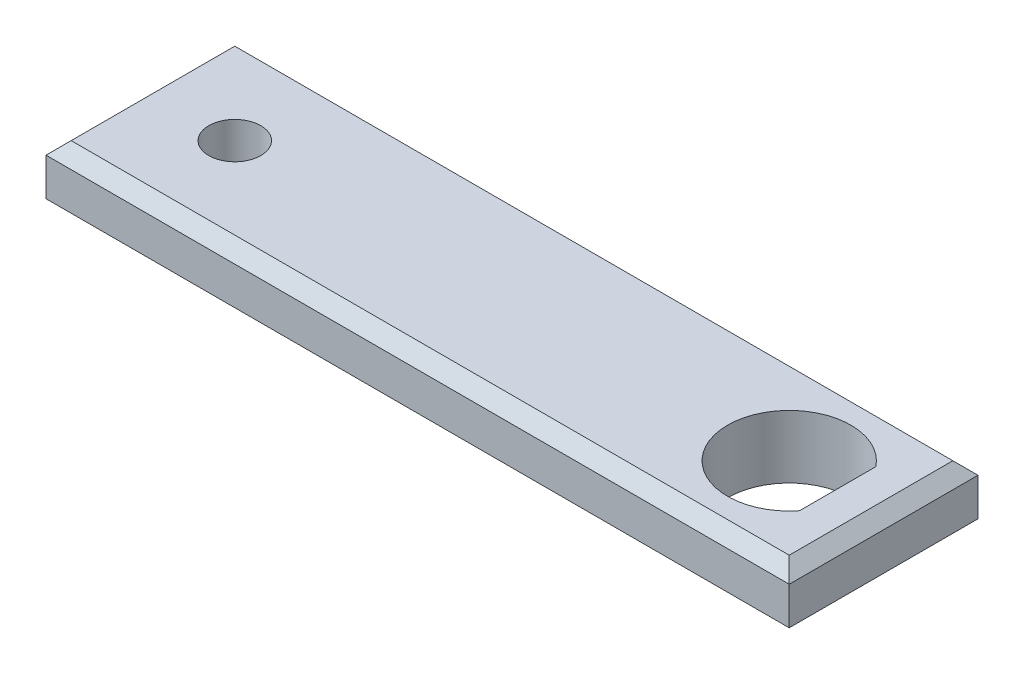
SolidWorks part; units mm, degrees
ref_plane "Front" through (0, 0, 0) normal (0, 0, 1) x (1, 0, 0)
ref_plane "Top" through (0, 0, 0) normal (0, 1, 0) x (-1, 0, 0)
ref_plane "Right" through (0, 0, 0) normal (1, 0, 0) x (0, 0, -1)
sketch "Sketch1" plane through (0, 0, 0) normal (0, 0, 1) x (1, 0, 0)
  line L0 (0, 0) -> (75, 0)
  line L1 (0, 0) -> (0, 6.35)
  line L2 (75, 6.35) -> (0, 6.35)
  line L3 (75, 6.35) -> (75, 0)
  dimension "D1" = 6.35
  dimension "D2" = 75
extrude "Base-Extrude" add sketch "Sketch1" along normal blind 19.05
sketch "Sketch2" plane through (0, 6.35, 0) normal (0, 1, 0) x (-1, 0, 0)
  line L0 (-75, 19.05) -> (-75, 0) construction
  line L1 (-75, 19.05) -> (0, 19.05) construction
  line L2 (-70.3645, 5.6755) -> (-70.3645, 13.3745)
  arc A0 (-70.3645, 5.6755) -> (-70.3645, 13.3745) centre (-65.475, 9.525) ccw
  dimension "D1" = 12.446
  dimension "D2" = 9.525
  dimension "D3" = 9.525
  dimension "D4" = 4.8895
extrude "Cut-Extrude1" cut sketch "Sketch2" against normal through all
sketch "Sketch3" plane through (0, 6.35, 0) normal (0, 1, 0) x (-1, 0, 0)
  line L0 (0, 19.05) -> (0, 0) construction
  circle A0 centre (-9.525, 9.525) radius 2.6225
  arc A1 (-70.3645, 5.6755) -> (-70.3645, 13.3745) centre (-65.475, 9.525) ccw construction
  point P5 (-65.475, 9.525)
  dimension "D2" = 9.525
extrude "Cut-Extrude2" cut sketch "Sketch3" against normal through all
chamfer "Chamfer1" distance 1.27 angle 45 8 edges at (75, 6.35, 9.525) (37.5, 6.35, 19.05) (0, 6.35, 9.525) (37.5, 6.35, 0) (75, 0, 9.525) (37.5, 0, 19.05) (0, 0, 9.525) (37.5, 0, 0)
